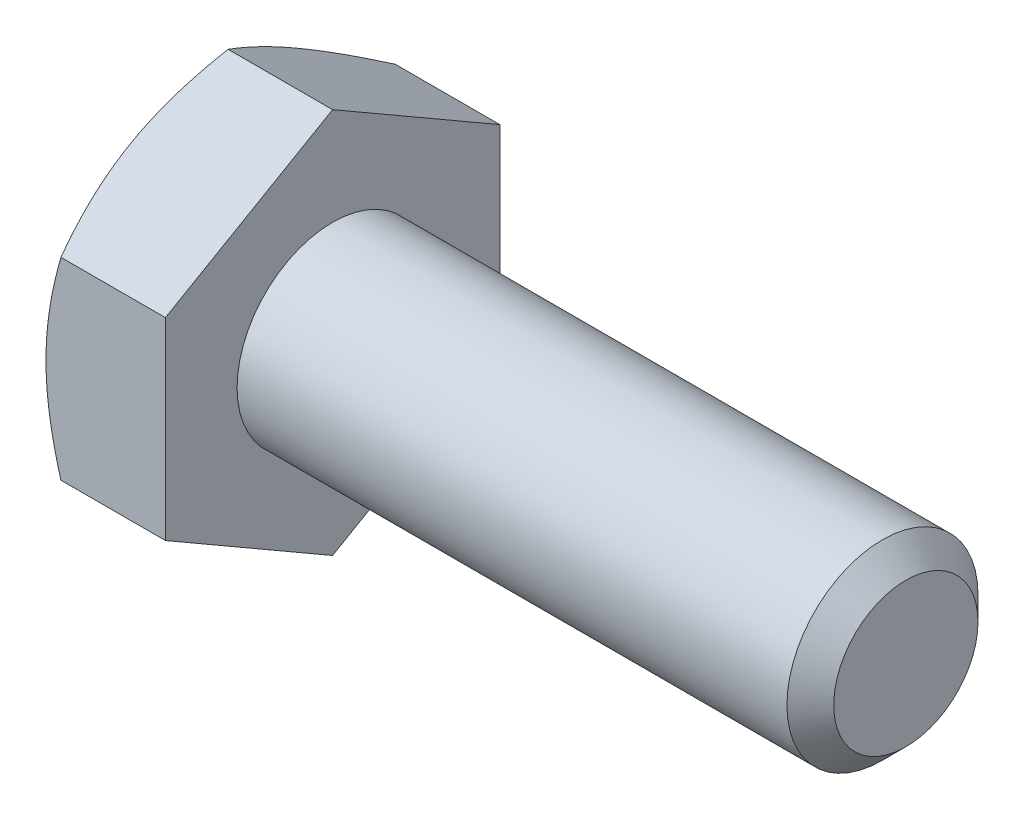
SolidWorks part; units mm, degrees
material "Alloy Steel"
ref_plane "Front Plane" through (0, 0, 0) normal (0, 0, 1) x (1, 0, 0)
ref_plane "Top Plane" through (0, 0, 0) normal (0, 1, 0) x (1, 0, 0)
ref_plane "Right Plane" through (0, 0, 0) normal (1, 0, 0) x (0, 0, -1)
sketch "Sketch1" plane through (0, 0, 0) normal (0, 0, 1) x (1, 0, 0)
  line L0 (-11.5094, 0) -> (11.5094, 0) construction
  line L1 (11.5094, 3.175) -> (11.5094, -3.175) construction
  line L2 (-7.5406, 5.5562) -> (-7.5406, -5.5562) construction
  line L3 (-11.5094, 5.5562) -> (-11.5094, -5.5562) construction
  point P9 (-7.5406, 0)
  point P10 (7.0644, -3.175)
  dimension "D1" = 4.445
  dimension "Screw Dia" = 6.35
  dimension "Hex" = 11.1125
  dimension "Head Ht" = 3.9688
  dimension "Screw Lenght" = 19.05
ref_plane "Plane2" through (11.5094, 0, 0) normal (1, 0, 0) x (0, 0, -1)
sketch "Sketch5" plane through (11.5094, 0, 0) normal (1, 0, 0) x (0, 0, -1)
  circle A0 centre (0, 0) radius 3.175
extrude "Boss-Extrude3" add sketch "Sketch5" against normal up to vertex (19.05 mm away) up to point (-7.5406, 0, 0)
sketch "Sketch9" plane through (11.5094, 0, 0) normal (1, 0, 0) x (0, 0, -1)
  circle A1 centre (0, 0) radius 3.175
  circle A2 centre (0, 0) radius 3.175
  dimension "D1" = 0
curve "Helix/Spiral1" pitch 1.27 height 20.32 turns 16 parameters "Pitch"=1.27
chamfer "Chamfer1" distance 0.7772 angle 45 1 edges at (11.5094, 0, -3.175)
sketch "Sketch10" plane through (0, 0, 0) normal (0, 0, 1) x (1, 0, 0)
  line L0 (11.5094, 3.175) -> (11.9856, 2.3501)
  line L1 (11.9856, 2.3501) -> (12.1444, 2.3501)
  line L2 (12.1444, 2.3501) -> (12.6206, 3.175)
  line L3 (11.5094, 3.175) -> (12.6206, 3.175)
  line L4 (12.065, 3.175) -> (12.065, 2.3501) construction
  line L5 (11.7475, 2.7626) -> (12.3825, 2.7626) construction
  dimension "D1" = 60
  dimension "D2" = 0.1588
  dimension "D3" = 0.635
sketch "Sketch6" plane through (-7.5406, 0, 0) normal (-1, 0, 0) x (0, 0, 1)
  line L0 (0, 5.5562) -> (0, -5.5562) construction
  line L1 (5.5563, 3.2079) -> (0, 6.4158)
  line L2 (0, 6.4158) -> (-5.5562, 3.2079)
  line L3 (-5.5562, 3.2079) -> (-5.5562, -3.2079)
  line L4 (-5.5562, -3.2079) -> (0, -6.4158)
  line L5 (0, -6.4158) -> (5.5563, -3.2079)
  line L6 (5.5563, -3.2079) -> (5.5563, 3.2079)
  circle A0 centre (0, 0) radius 5.5563 construction
extrude "Boss-Extrude4" add sketch "Sketch6" along normal up to vertex (3.9688 mm away) up to point (-11.5094, -5.5562, 0)
sketch "Sketch7" plane through (-11.5094, 0, 0) normal (-1, 0, 0) x (0, 0, 1)
  circle A0 centre (0, 0) radius 5.5563 construction
  circle A1 centre (0, 0) radius 5.5563
sketch "Sketch8" plane through (-11.5094, 0, 0) normal (-1, 0, 0) x (0, 0, 1)
  circle A0 centre (0, 0) radius 5.5563 construction
  circle A1 centre (0, 0) radius 5.5563
extrude "Cut-Extrude3" cut sketch "Sketch8" against normal through all draft 60 flip side to cut
sketch "Sketch12" plane through (-11.5094, 0, 0) normal (-1, 0, 0) x (0, 0, 1)
  line L0 (0, 4.2783) -> (0, 2.3892) construction
  line L1 (0.1667, 4.2783) -> (0.1667, 2.3892)
  line L2 (-0.1667, 4.2783) -> (-0.1667, 2.3892)
  line L3 (0, 3.175) -> (0, -3.175) construction
  arc A0 (0.1667, 4.2783) -> (-0.1667, 4.2783) centre (0, 4.2783) ccw
  arc A1 (-0.1667, 2.3892) -> (0.1667, 2.3892) centre (0, 2.3892) ccw
  circle A3 centre (0, 0) radius 2.2225 construction
  circle A4 centre (0, 0) radius 4.445 construction
  point P2 (0, 3.3337)
  dimension "D1" = 4.445
  dimension "D3" = 8.89
  dimension "D2" = 0.3334
extrude "Cut-Extrude4" cut sketch "Sketch12" against normal blind 0.254
pattern_circular "CirPattern1" count 3 over 360 about axis through (0, 0, 0) along (1, 0, 0) of "Cut-Extrude4"
equation "\"D2@Sketch10\" = \"Pitch@Helix/Spiral1\"*.125"
equation "\"D3@Sketch10\" = \"Pitch@Helix/Spiral1\"*.5"
equation "\"D1@Chamfer1\" = \"Pitch@Helix/Spiral1\"*.612"
equation "\"D1@Sketch12\" = \"Hex@Sketch1\"*.4"
equation "\"D3@Sketch12\" = \"Hex@Sketch1\"*.8"
equation "\"D2@Sketch12\" = \"Hex@Sketch1\"*.03"
equation "\"D1@Sketch1\" = \"Pitch@Helix/Spiral1\"*3.5"
equation "\"D3@Helix/Spiral1\" = \"Screw Lenght@Sketch1\"+\"Pitch@Helix/Spiral1\""
